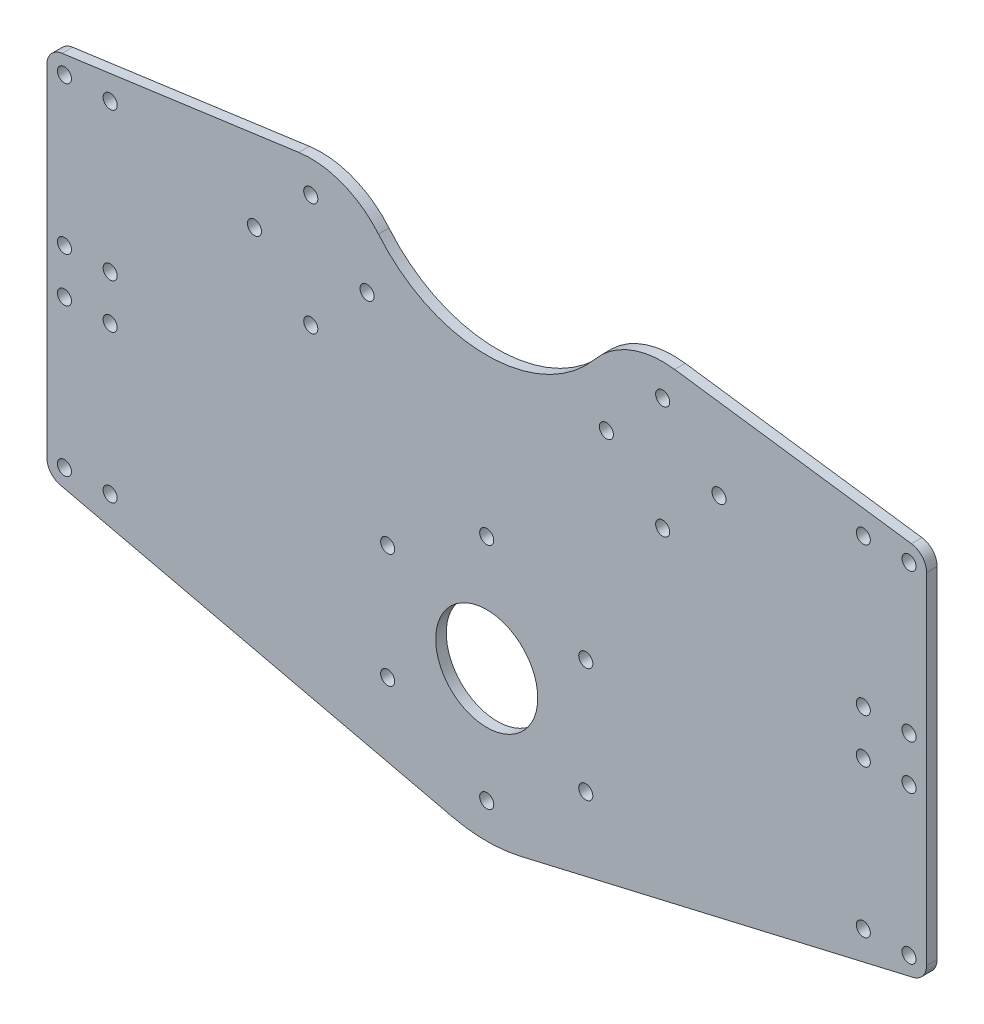
SolidWorks part; units mm, degrees
material "1060 Alloy"
ref_plane "Front Plane" through (0, 0, 0) normal (0, 0, 1) x (1, 0, 0)
ref_plane "Top Plane" through (0, 0, 0) normal (0, 1, 0) x (1, 0, 0)
ref_plane "Right Plane" through (0, 0, 0) normal (1, 0, 0) x (0, 0, -1)
sketch "Sketch1" plane through (0, 0, 0) normal (0, 0, 1) x (1, 0, 0)
  line L1 (-125, 10.5588) -> (-125, -86.1125)
  line L2 (-121.134, -90.9822) -> (-9.6391, -116.9462)
  line L3 (-120.6814, 15.5122) -> (-53.407, 24.7668)
  line L4 (125, 10.5588) -> (125, -86.1125)
  line L5 (121.134, -90.9822) -> (9.6391, -116.9462)
  line L6 (120.6814, 15.5122) -> (53.407, 24.7668)
  line L7 (-50, 0) -> (50, 0) construction
  line L8 (0, -75.5537) -> (0, 0) construction
  arc A0 (-30.7692, 15.9743) -> (-53.407, 24.7668) centre (-50, 0) ccw
  arc A1 (53.407, 24.7668) -> (30.7692, 15.9743) centre (50, 0) ccw
  arc A2 (-9.6391, -116.9462) -> (9.6391, -116.9462) centre (0, -75.5537) ccw
  circle A13 centre (0, -75.5537) radius 14.5
  arc A14 (-30.7692, 15.9743) -> (30.7692, 15.9743) centre (0, 41.5331) ccw
  arc A15 (125, 10.5588) -> (120.6814, 15.5122) centre (120, 10.5588) ccw
  arc A16 (125, -86.1125) -> (121.134, -90.9822) centre (120, -86.1125) cw
  arc A17 (-125, -86.1125) -> (-121.134, -90.9822) centre (-120, -86.1125) ccw
  arc A18 (-125, 10.5588) -> (-120.6814, 15.5122) centre (-120, 10.5588) cw
  point P18 (0, -37.7768)
  point P19 (125, -37.7768)
  point P29 (125, 14.9181)
  point P33 (125, -90.0819)
  point P36 (-125, -90.0819)
  point P39 (-125, 14.9181)
  dimension "D3" = 50
  dimension "D4" = 50
  dimension "D5" = 85
  dimension "D6" = 120
  dimension "D8" = 50
  dimension "D11" = 29
  dimension "D9" = 80
  dimension "D13" = 5
  dimension "D1" = 100
  dimension "D2" = 120
  dimension "D7" = 105
  dimension "D12" = 90.6
extrude "Boss-Extrude1" add sketch "Sketch1" along normal blind 3
hole_wizard "M4 Clearance Hole1" positions "Sketch5" profile "Sketch3" hole size "M4" standard "ISO"
sketch "Sketch5" plane through (0, 0, 3) normal (0, 0, 1) x (1, 0, 0)
  line L0 (-50, 0) -> (50, 0) construction
  circle A0 centre (-50, 0) radius 16 construction
  circle A1 centre (50, 0) radius 16 construction
  point P0 (-66, 0)
  point P16 (0, 0)
  point P17 (-34, 0)
  point P19 (-50, 16)
  point P21 (-50, -16)
  point P23 (34, 0)
  point P25 (50, 16)
  point P27 (66, 0)
  point P29 (50, -16)
  dimension "D1" = 32
  dimension "D2" = 100
sketch "Sketch3" plane through (-66, 0, 3) normal (1, 0, 0) x (0, -1, 0)
  line L0 (0, 0) -> (0, 11.2017)
  line L1 (0, 11.2017) -> (2, 10)
  line L2 (2, 10) -> (2, 0)
  line L5 (2, 0) -> (0, 0)
  line L10 (0, 11.2017) -> (-2, 10) construction
  line L11 (0, -6.35) -> (0, 107.95) construction
  dimension "Hole Dia." = 4
  dimension "Hole Depth" = 10
  dimension "Drill Angle" = 118
hole_wizard "M4 Clearance Hole2" positions "Sketch7" profile "Sketch8" hole size "M4" standard "ISO"
sketch "Sketch7" plane through (0, 0, 3) normal (0, 0, 1) x (1, 0, 0)
  circle A0 centre (0, -75.5537) radius 32.5 construction
  point P0 (0, -108.0537)
  dimension "D1" = 65
sketch "Sketch8" plane through (0, -108.0537, 3) normal (1, 0, 0) x (0, -1, 0)
  line L0 (0, 0) -> (0, 11.2017)
  line L1 (0, 11.2017) -> (2, 10)
  line L2 (2, 10) -> (2, 0)
  line L5 (2, 0) -> (0, 0)
  line L10 (0, 11.2017) -> (-2, 10) construction
  line L11 (0, -6.35) -> (0, 107.95) construction
  dimension "Hole Dia." = 4
  dimension "Hole Depth" = 10
  dimension "Drill Angle" = 118
pattern_circular "CirPattern1" count 6 over 360 about axis through (0, -75.5537, 0) along (0, 0, 1) of "M4 Clearance Hole2"
hole_wizard "M4 Clearance Hole3" positions "Sketch9" profile "Sketch10" hole size "M4" standard "ISO" end condition through all
sketch "Sketch9" plane through (0, 0, 3) normal (0, 0, 1) x (1, 0, 0)
  line L1 (-120, 10.5588) -> (-107, 10.5588) construction
  line L2 (-120, 10.5588) -> (-120, -31.4412) construction
  line L3 (-120, -31.4412) -> (-107, -31.4412) construction
  line L4 (-107, 10.5588) -> (-107, -31.4412) construction
  line L6 (-120, -86.1125) -> (-107, -86.1125) construction
  line L7 (-120, -86.1125) -> (-120, -44.1125) construction
  line L8 (-120, -44.1125) -> (-107, -44.1125) construction
  line L9 (-107, -86.1125) -> (-107, -44.1125) construction
  line L11 (120, 10.5588) -> (107, 10.5588) construction
  line L12 (120, 10.5588) -> (120, -31.4412) construction
  line L13 (120, -31.4412) -> (107, -31.4412) construction
  line L14 (107, 10.5588) -> (107, -31.4412) construction
  line L16 (120, -86.1125) -> (107, -86.1125) construction
  line L17 (120, -86.1125) -> (120, -44.1125) construction
  line L18 (120, -44.1125) -> (107, -44.1125) construction
  line L19 (107, -86.1125) -> (107, -44.1125) construction
  arc A0 (-120.6814, 15.5122) -> (-125, 10.5588) centre (-120, 10.5588) ccw construction
  arc A1 (-125, -86.1125) -> (-121.134, -90.9822) centre (-120, -86.1125) ccw construction
  arc A2 (125, 10.5588) -> (120.6814, 15.5122) centre (120, 10.5588) ccw construction
  point P0 (-120, 10.5588)
  point P2 (-107, 10.5588)
  point P4 (-120, -31.4412)
  point P6 (-107, -31.4412)
  point P119 (-120, -86.1125)
  point P120 (-107, -44.1125)
  point P191 (-120, -44.1125)
  point P192 (-107, -86.1125)
  point P208 (120, 10.5588)
  point P209 (107, -31.4412)
  point P292 (120, -31.4412)
  point P293 (107, 10.5588)
  point P295 (120, -86.1125)
  point P296 (107, -44.1125)
  point P411 (120, -44.1125)
  point P412 (107, -86.1125)
  dimension "D1" = 42
  dimension "D2" = 13
sketch "Sketch10" plane through (-120, 10.5588, 3) normal (1, 0, 0) x (0, -1, 0)
  line L0 (0, 0) -> (0, 3)
  line L1 (0, 3) -> (2, 3)
  line L2 (2, 3) -> (2, 0)
  line L5 (2, 0) -> (0, 0)
  line L11 (0, -6.35) -> (0, 107.95) construction
  dimension "Thru Hole Dia." = 4
  dimension "Thru Hole Depth" = 3
